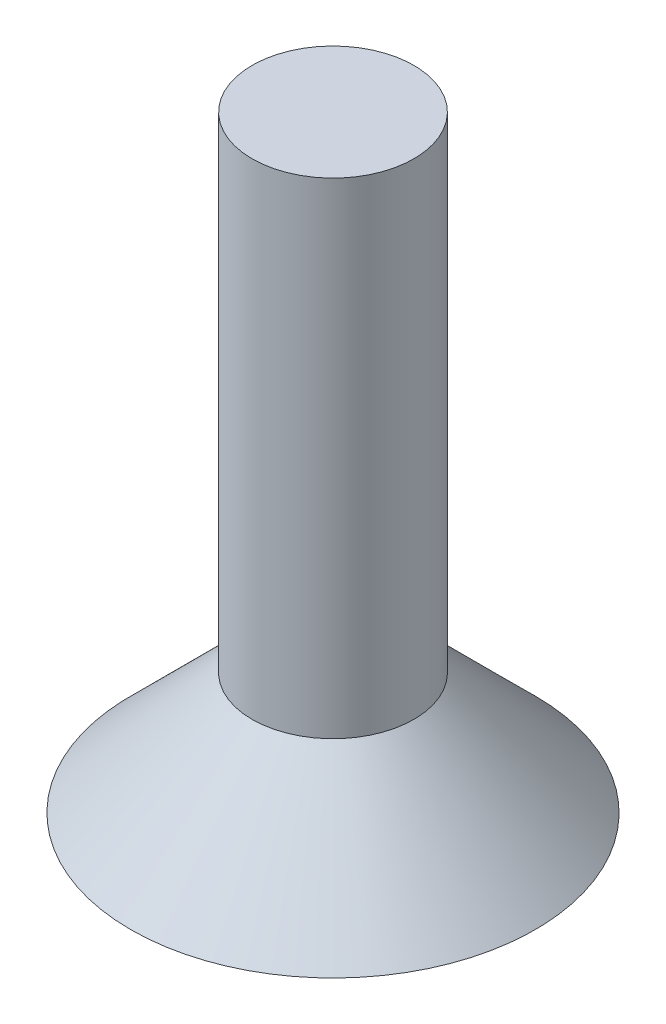
SolidWorks part; units mm, degrees
ref_plane "Спереди" through (0, 0, 0) normal (0, 0, 1) x (1, 0, 0)
ref_plane "Сверху" through (0, 0, 0) normal (0, 1, 0) x (1, 0, 0)
ref_plane "Справа" through (0, 0, 0) normal (1, 0, 0) x (0, 0, -1)
sketch "Эскиз1" plane through (0, 0, 0) normal (0, 0, 1) x (1, 0, 0)
  line L0 (0, 15) -> (2, 15)
  line L1 (2, 15) -> (2, 3)
  line L2 (2, 3) -> (5, 0)
  line L3 (5, 0) -> (0, 0)
  line L4 (0, 49.838) -> (0, -6.7101) construction
  line L5 (0, 15) -> (0, 0)
  point P2 (0, 0)
  point P9 (0, 0)
revolve "Повернуть1" add sketch "Эскиз1" angle 360 about L4
